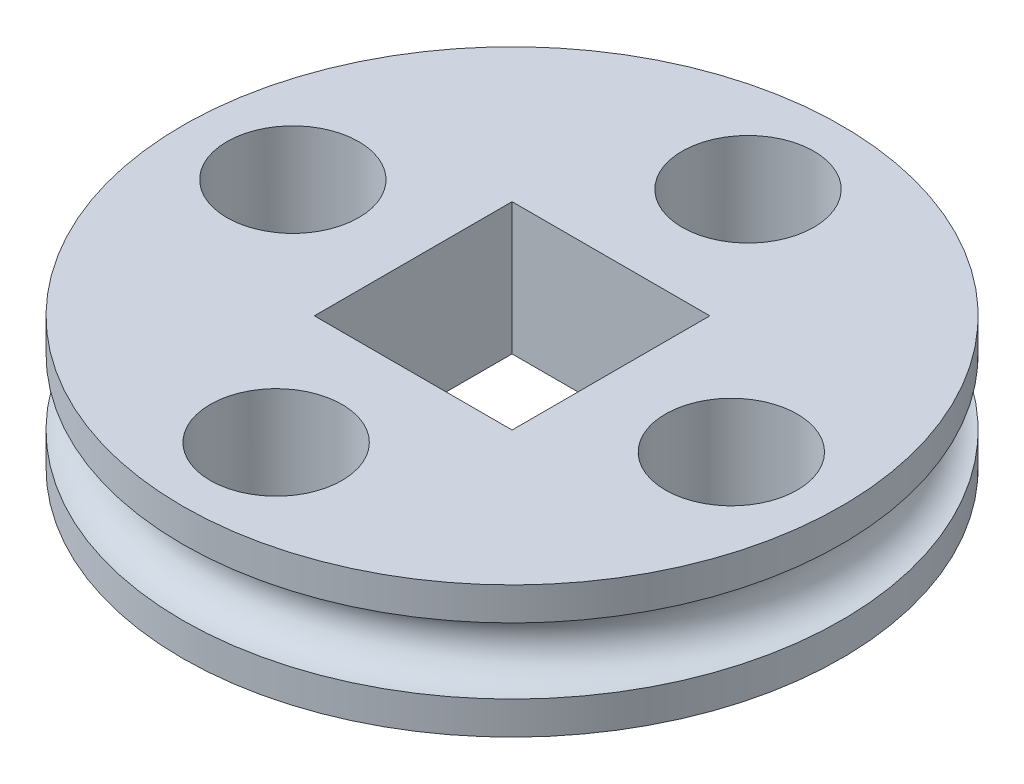
SolidWorks part; units mm, degrees
ref_plane "Ebene vorne" through (0, 0, 0) normal (0, 0, 1) x (1, 0, 0)
ref_plane "Ebene oben" through (0, 0, 0) normal (0, 1, 0) x (1, 0, 0)
ref_plane "Ebene rechts" through (0, 0, 0) normal (1, 0, 0) x (0, 0, -1)
sketch "Skizze1" plane through (0, 0, 0) normal (0, 1, 0) x (1, 0, 0)
  circle A0 centre (0, 0) radius 5
extrude "Aufsatz-Linear austragen1" add sketch "Skizze1" along normal blind 2
sketch "Skizze3" plane through (0, 2, 0) normal (0, 1, 0) x (1, 0, 0)
  line L0 (1.5, 1.5) -> (-1.5, 1.5)
  line L1 (1.5, 1.5) -> (1.5, -1.5)
  line L2 (1.5, -1.5) -> (-1.5, -1.5)
  line L3 (-1.5, 1.5) -> (-1.5, -1.5)
  line L4 (0, 0) -> (0, -3) construction
  line L5 (0, 0) -> (-10.1495, 0) construction
  point P8 (-1.5, 0)
  point P9 (0, -1.5)
extrude "Schnitt-Linear austragen1" cut sketch "Skizze3" against normal blind 3
sketch "Skizze4" plane through (0, 2, 0) normal (0, 1, 0) x (1, 0, 0)
  circle A0 centre (3.4528, -0.1264) radius 1
extrude "Schnitt-Linear austragen2" cut sketch "Skizze4" against normal blind 3
pattern_circular "Kreismuster1" count 4 over 360 about axis through (0, 0, 0) along (0, 1, 0) of "Schnitt-Linear austragen2"
sketch "Skizze6" plane through (0, 0, 0) normal (0, 0, 1) x (1, 0, 0)
  line L5 (-5, 2) -> (-5, 0) construction
  line L6 (-5, 1.5) -> (-5, 0.5)
  arc A0 (-5, 1.5) -> (-5, 0.5) centre (-5, 1) cw
revolve "Schnitt-Rotation2" cut sketch "Skizze6" angle 360 about axis through (0, 2, 0) along (0, -1, 0)
